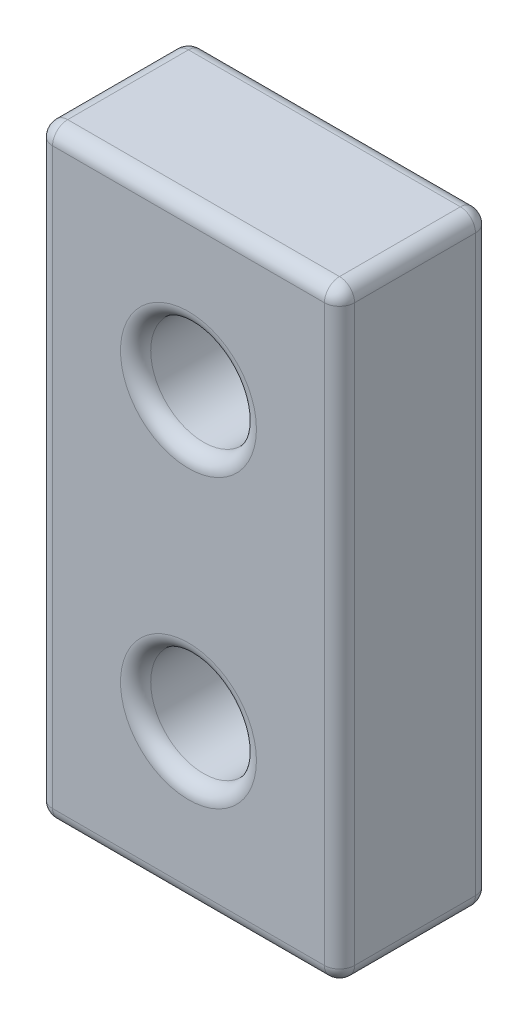
SolidWorks part; units mm, degrees
ref_plane "Front Plane" through (0, 0, 0) normal (0, 0, 1) x (1, 0, 0)
ref_plane "Top Plane" through (0, 0, 0) normal (0, 1, 0) x (1, 0, 0)
ref_plane "Right Plane" through (0, 0, 0) normal (1, 0, 0) x (0, 0, -1)
sketch "Sketch1" plane through (0, 0, 0) normal (0, 0, 1) x (1, 0, 0)
  line L0 (0, 9.5) -> (0, -9.5) construction
  line L1 (-9, -20) -> (9, -20)
  line L2 (-10, -19) -> (-10, 19)
  line L3 (-9, 20) -> (9, 20)
  line L4 (10, -19) -> (10, 19)
  line L5 (-10, -20) -> (10, 20) construction
  line L6 (-10, 20) -> (10, -20) construction
  arc A0 (9, -20) -> (10, -19) centre (9, -19) ccw
  arc A1 (-9, -20) -> (-10, -19) centre (-9, -19) cw
  arc A2 (9, 20) -> (10, 19) centre (9, 19) cw
  arc A3 (-10, 19) -> (-9, 20) centre (-9, 19) cw
  point P0 (0, 0)
  point P8 (0, -13.4302)
  point P9 (0, 0)
  dimension "D4" = 1
  dimension "D1" = 20
  dimension "D2" = 40
  dimension "D3" = 19
extrude "Boss-Extrude1" add sketch "Sketch1" along normal blind 10
hole_wizard "M8x1.0 Tapped Hole1" positions "Sketch2" profile "Sketch3" tap size "M8x1.0" standard "ANSI Metric" end condition through all
sketch "Sketch2" plane through (0, 0, 0) normal (0, 0, -1) x (-1, 0, 0)
  point P0 (0, 9.5)
  point P3 (0, -9.5)
sketch "Sketch3" plane through (0, 9.5, 0) normal (1, 0, 0) x (0, 1, 0)
  line L0 (0, 0) -> (0, 10)
  line L1 (0, 10) -> (3.5, 10)
  line L2 (3.5, 10) -> (3.5, 0.525)
  line L3 (3.5, 0.525) -> (4.025, 0)
  line L5 (4.025, 0) -> (0, 0)
  line L6 (-3.5, 0.525) -> (-4.025, 0) construction
  line L11 (0, -6.35) -> (0, 107.95) construction
  dimension "Thru Tap Drill Dia." = 7
  dimension "Thru Tap Drill Depth" = 10
  dimension "Near C'Sink Dia." = 8.05
  dimension "Near C'Sink Angle" = 90
cosmetic thread "Hole Thread1" parameters "D2"=8
cosmetic thread "Hole Thread2" parameters "D2"=8
fillet "Fillet1" radius 1 20 edges at (0, -20, 10) (-9.7071, -19.7071, 10) (-10, 0, 10) (-9.7071, 19.7071, 10) (0, 20, 10) (9.7071, 19.7071, 10) (10, 0, 10) (9.7071, -19.7071, 10) (-3.5, -9.5, 10) (-3.5, 9.5, 10) (10, 0, 0) (9.7071, 19.7071, 0) (0, 20, 0) (-9.7071, 19.7071, 0) (-10, 0, 0) (-9.7071, -19.7071, 0) (0, -20, 0) (9.7071, -19.7071, 0) (-4.025, -9.5, 0) (-4.025, 9.5, 0)
